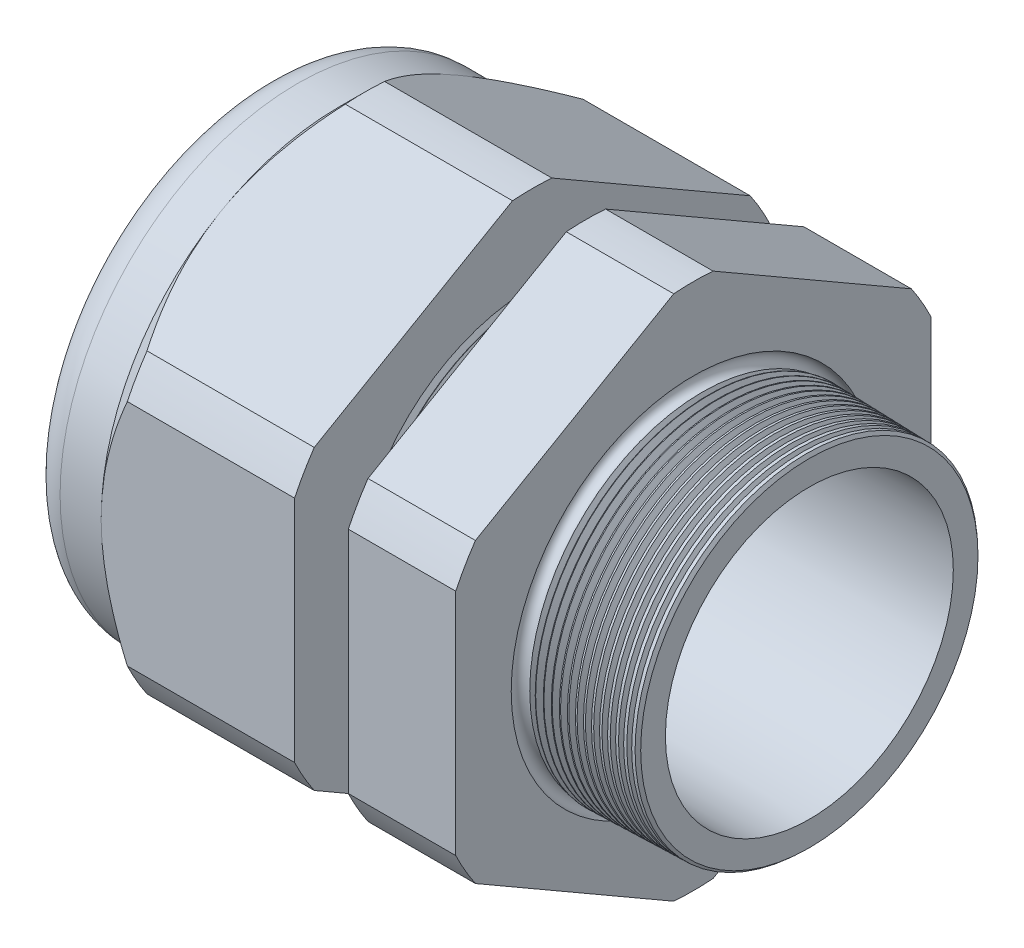
SolidWorks part; units mm, degrees
ref_plane "Front Plane" through (0, 0, 0) normal (0, 0, 1) x (1, 0, 0)
ref_plane "Top Plane" through (0, 0, 0) normal (0, 1, 0) x (1, 0, 0)
ref_plane "Right Plane" through (0, 0, 0) normal (1, 0, 0) x (0, 0, -1)
sketch "Sketch10" plane through (0, 0, 0) normal (0, 0, 1) x (1, 0, 0)
  line L0 (0, 0) -> (-115.3565, 0) construction
  line L1 (-55.88, 16.002) -> (-25.8776, 16.002)
  line L2 (5.08, 16.0803) -> (5.08, 19.1283)
  line L3 (-7.874, 19.4676) -> (5.08, 19.1283)
  line L4 (-7.874, 53.086) -> (-7.874, 19.4676)
  line L5 (-7.874, 53.086) -> (-19.874, 53.086)
  line L6 (-19.874, 53.086) -> (-19.874, 19.7818)
  line L7 (-25.8776, 19.939) -> (-19.874, 19.7818)
  line L8 (-25.8776, 19.939) -> (-25.8776, 53.086)
  line L9 (-25.8776, 53.086) -> (-47.48, 53.086)
  line L10 (-47.48, 53.086) -> (-47.48, 26.543)
  line L11 (-47.48, 26.543) -> (-55.88, 26.543)
  line L12 (-55.88, 26.543) -> (-55.88, 16.002)
  line L13 (-25.8776, 16.002) -> (5.08, 16.0803)
  dimension "D1" = 60.96
  dimension "D2" = 32.004
  dimension "D3" = 1.5
  dimension "D4" = 3.048
  dimension "A" = 39.878
  dimension "D6" = 53.086
  dimension "D8" = 106.172
  dimension "D9" = 8.4
  dimension "D10" = 21.6024
  dimension "D11" = 12
  dimension "D" = 12.954
revolve "Revolve2" add sketch "Sketch10" angle 360 about L0
sketch "Sketch12" plane through (-47.48, 0, 0) normal (-1, 0, 0) x (0, 0, 1)
  line L1 (-2.1972, 29.3807) -> (-24.3458, 16.5931)
  line L2 (-26.543, 12.7876) -> (-26.543, -12.7876)
  line L3 (-24.3458, -16.5931) -> (-2.1972, -29.3807)
  line L4 (2.1972, -29.3807) -> (24.3458, -16.5931)
  line L5 (26.543, -12.7876) -> (26.543, 12.7876)
  line L6 (24.3458, 16.5931) -> (2.1972, 29.3807)
  circle A0 centre (0, 0) radius 26.543 construction
  arc A1 (2.1972, 29.3807) -> (-2.1972, 29.3807) centre (0, 0) ccw
  arc A2 (-24.3458, 16.5931) -> (-26.543, 12.7876) centre (0, 0) ccw
  arc A3 (-26.543, -12.7876) -> (-24.3458, -16.5931) centre (0, 0) ccw
  arc A4 (-2.1972, -29.3807) -> (2.1972, -29.3807) centre (0, 0) ccw
  arc A5 (24.3458, -16.5931) -> (26.543, -12.7876) centre (0, 0) ccw
  arc A6 (26.543, 12.7876) -> (24.3458, 16.5931) centre (0, 0) ccw
  dimension "D2" = 58.9255
  dimension "D1" = 53.086
extrude "Cut-Extrude2" cut sketch "Sketch12" against normal through all flip side to cut
fillet "Fillet4" radius 3.81 1 edges at (-55.88, 0, -26.543)
sketch "Sketch19" plane through (-47.48, 0, 0) normal (-1, 0, 0) x (0, 0, 1)
  line L0 (26.543, 0) -> (26.543, 12.7876) construction
  circle A0 centre (0, 0) radius 26.543
extrude "Cut-Extrude3" cut sketch "Sketch19" against normal blind 3.998 draft 45 flip side to cut
chamfer "Chamfer1" distance 0.254 angle 45 1 edges at (5.08, 0, -19.1283)
sketch "Sketch21" plane through (-55.88, 0, 0) normal (-1, 0, 0) x (0, 0, 1)
  circle A0 centre (0, 0) radius 16.002
  circle A2 centre (0, 0) radius 16.002 construction
extrude "plug" add sketch "Sketch21" against normal blind 12.7 separate body
sketch "Sketch22" plane through (-55.88, 0, 0) normal (-1, 0, 0) x (0, 0, 1)
  circle A0 centre (0, 0) radius 15.748
  circle A1 centre (0, 0) radius 16.002 construction
  dimension "D1" = 0.254
extrude "Cut-Extrude4" cut sketch "Sketch22" against normal blind 0.508
sketch "Sketch27" plane through (-55.372, 0, 0) normal (-1, 0, 0) x (0, 0, 1)
  line L0 (-4.3624, 0) -> (4.3624, 0) construction
  circle A0 centre (-11.2852, 0) radius 4.445
  circle A1 centre (0, 0) radius 15.748 construction
  dimension "D1" = 0.0178
  dimension "holedia" = 8.89
extrude "plugholes" cut sketch "Sketch27" against normal through all
pattern_circular "CirPattern1" count 7 over 360 about axis through (0, 0, 0) along (1, 0, 0) of "plugholes"
sketch "Sketch28" [suppressed] plane through (-38.354, 0, 0) normal (-1, 0, 0) x (0, 0, 1)
  circle A0 centre (0, 0) radius 1.905
  dimension "midholedia" = 8.89
extrude "midhole" [suppressed] cut sketch "Sketch28" against normal through all
sketch "Sketch29" plane through (0, 0, 0) normal (0, 0, 1) x (1, 0, 0)
  line L0 (-25.8776, 19.939) -> (-25.1446, 19.9198)
  line L1 (-19.874, 19.7818) -> (-25.8776, 19.939) construction
  line L2 (-25.1446, 19.9198) -> (-25.5277, 19.2946)
  line L3 (-25.5277, 19.2946) -> (-25.8776, 19.939)
  dimension "D1" = 60
  dimension "D2" = 60
  dimension "D3" = 0.635
revolve "Cut-Revolve1" cut sketch "Sketch29" angle 360 about axis through (0, 0, 0) along (-1, 0, 0)
pattern_linear "LPattern1" count 8 spacing 0.762 along (1, 0, 0) of "Cut-Revolve1"
sketch "Sketch30" plane through (0, 0, 0) normal (0, 0, 1) x (1, 0, 0)
  line L0 (-7.874, 19.4676) -> (-6.9944, 19.4445)
  line L1 (-7.874, 29.3807) -> (-7.874, 16.5931) construction
  line L2 (4.8261, 19.135) -> (-7.874, 19.4676) construction
  line L3 (-6.9944, 19.4445) -> (-7.4542, 18.6943)
  line L4 (-7.4542, 18.6943) -> (-7.874, 19.4676)
  dimension "D1" = 60
  dimension "D2" = 60
  dimension "D3" = 0.762
revolve "Cut-Revolve2" cut sketch "Sketch30" angle 360 about axis through (0, 0, 0) along (-1, 0, 0)
pattern_linear "LPattern2" count 15 spacing 0.889 along (1, 0, 0) of "Cut-Revolve2"
sketch "Sketch31" [suppressed] plane through (-38.354, 0, 0) normal (-1, 0, 0) x (0, 0, 1)
  line L0 (-1.905, 1.905) -> (1.905, 1.905)
  line L1 (-1.905, -1.905) -> (1.905, -1.905)
  circle A0 centre (0, 0) radius 1.905 construction
  arc A1 (-1.905, 1.905) -> (-1.905, -1.905) centre (-1.905, 0) ccw
  arc A2 (1.905, 1.905) -> (1.905, -1.905) centre (1.905, 0) cw
extrude "Cut-Extrude5" [suppressed] cut sketch "Sketch31" against normal through all
sketch "Sketch32" plane through (0, 0, 0) normal (0, 0, 1) x (1, 0, 0)
  line L0 (-7.874, 29.3807) -> (-7.874, 16.5931) construction
  circle A0 centre (-7.747, 19.4676) radius 0.889
  dimension "D2" = 1.778
  dimension "D1" = 0.127
revolve "Cut-Revolve3" cut sketch "Sketch32" angle 360 about axis through (0, 0, 0) along (-1, 0, 0)
